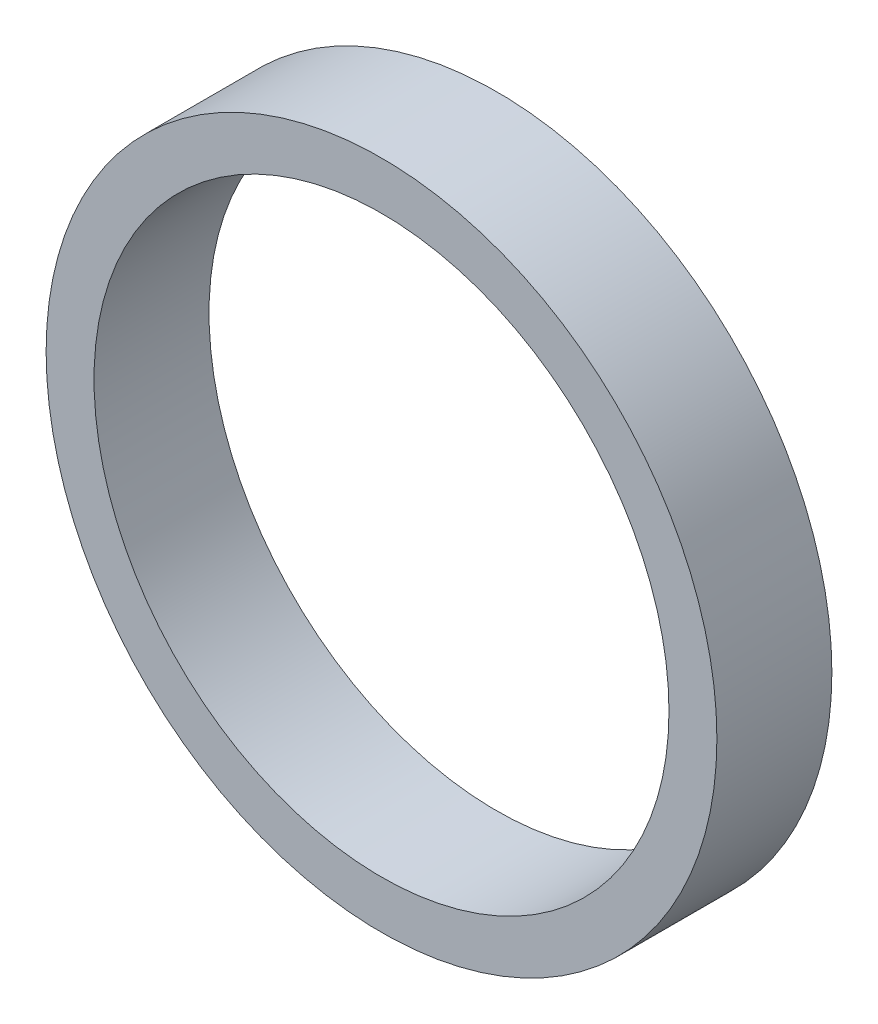
SolidWorks part; units mm, degrees
ref_plane "Alzado" through (0, 0, 0) normal (0, 0, 1) x (1, 0, 0)
ref_plane "Planta" through (0, 0, 0) normal (0, 1, 0) x (1, 0, 0)
ref_plane "Vista lateral" through (0, 0, 0) normal (1, 0, 0) x (0, 0, -1)
sketch "Croquis1" plane through (0, 0, 0) normal (0, 0, 1) x (1, 0, 0)
  circle A0 centre (0, 0) radius 15
  circle A1 centre (0, 0) radius 17.5
  dimension "D1" = 35
  dimension "D2" = 30
extrude "Saliente-Extruir1" add sketch "Croquis1" along normal blind 6
